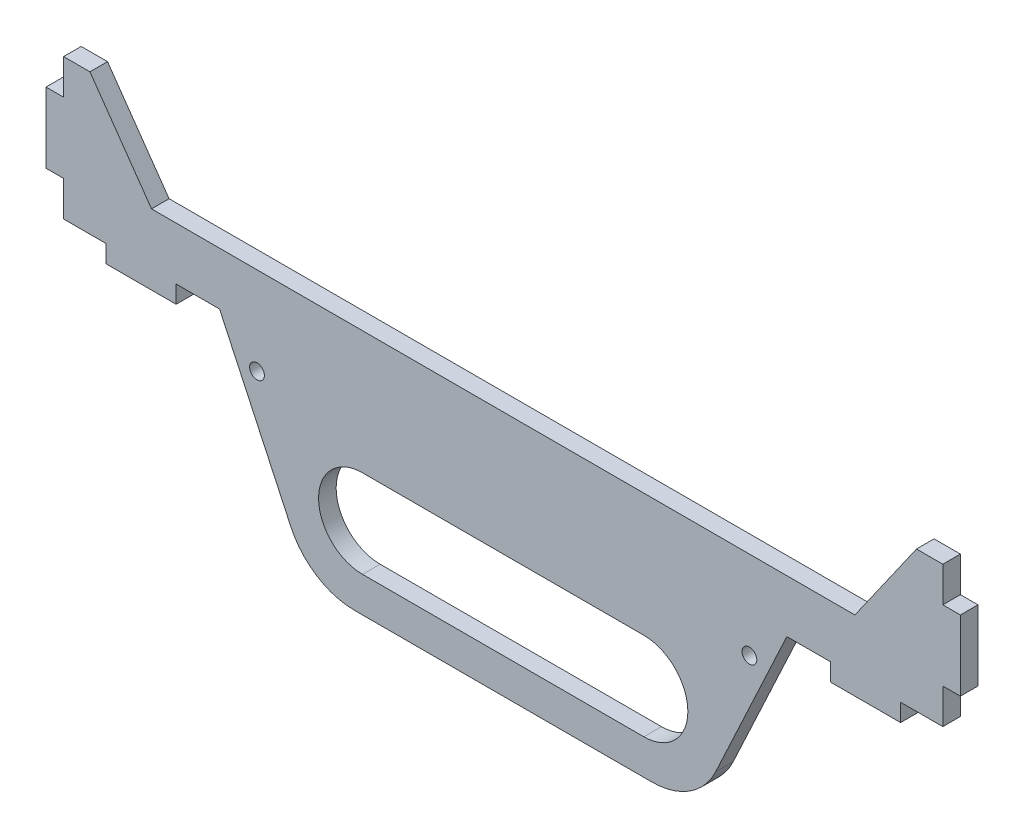
SolidWorks part; units mm, degrees
ref_plane "Front Plane" through (0, 0, 0) normal (0, 0, 1) x (1, 0, 0)
ref_plane "Top Plane" through (0, 0, 0) normal (0, 1, 0) x (1, 0, 0)
ref_plane "Right Plane" through (0, 0, 0) normal (1, 0, 0) x (0, 0, -1)
sketch "Sketch1" plane through (0, 0, 0) normal (0, 0, 1) x (1, 0, 0)
  line L0 (0, 0) -> (7.4948, 0)
  line L2 (7.4948, 0) -> (25, -25)
  line L3 (25, -25) -> (225, -25)
  line L4 (225, -25) -> (242.5052, 0)
  line L5 (242.5052, 0) -> (250, 0)
  line L7 (250, -40) -> (238, -40)
  line L9 (205.6469, -40) -> (180, -95)
  line L10 (180, -95) -> (70, -95)
  line L11 (70, -95) -> (44.3531, -40)
  line L12 (44.3531, -40) -> (32, -40)
  line L13 (0, -40) -> (0, -30)
  line L14 (0, -30) -> (-5, -30)
  line L16 (-5, -30) -> (-5, -10)
  line L17 (-5, -10) -> (0, -10)
  line L18 (0, -10) -> (0, 0)
  line L19 (250, -40) -> (250, -30)
  line L20 (250, -30) -> (255, -30)
  line L22 (255, -30) -> (255, -10)
  line L23 (255, -10) -> (250, -10)
  line L24 (250, -10) -> (250, 0)
  line L25 (85, -72.5) -> (165, -72.5) construction
  line L26 (85, -60) -> (165, -60)
  line L27 (85, -85) -> (165, -85)
  line L29 (218, -40) -> (205.6469, -40)
  line L30 (12, -40) -> (0, -40)
  line L31 (218, -40) -> (218, -45)
  line L32 (218, -45) -> (238, -45)
  line L33 (238, -40) -> (238, -45)
  line L35 (12, -40) -> (12, -45)
  line L36 (12, -45) -> (32, -45)
  line L37 (32, -40) -> (32, -45)
  arc A0 (85, -60) -> (85, -85) centre (85, -72.5) ccw
  arc A1 (165, -85) -> (165, -60) centre (165, -72.5) ccw
  point P34 (125, -72.5)
  dimension "D1" = 12.5
  dimension "D5" = 32
  dimension "D2" = 7.4948
  dimension "D3" = 12
  dimension "D4" = 25
  dimension "D6" = 44.3531
  dimension "D7" = 70
  dimension "D8" = 85
  dimension "D9" = 125
  dimension "D10" = 180
  dimension "D11" = 255
  dimension "D12" = 10
  dimension "D13" = 25
  dimension "D14" = 72.5
  dimension "D15" = 95
extrude "Boss-Extrude1" add sketch "Sketch1" along normal blind 5
fillet "Fillet1" radius 20 2 edges at (70, -95, 2.5) (180, -95, 2.5)
sketch "Sketch3" plane through (0, 0, 5) normal (0, 0, 1) x (1, 0, 0)
  line L0 (225, -25) -> (25, -25) construction
  line L1 (0, -50.4333) -> (0, -20.4333) construction
  circle A0 centre (55, -50) radius 2.1
  circle A1 centre (55, -50) radius 4 construction
  dimension "D1" = 4.2
  dimension "D2" = 8
  dimension "D3" = 25
  dimension "D4" = 55
extrude "Cut-Extrude1" cut sketch "Sketch3" against normal blind 5
ref_plane "Plane1" through (125, 0, 0) normal (-1, 0, 0) x (0, 0, 1)
mirror "Mirror1" about plane through (125, 0, 0) normal (-1, 0, 0) of "Cut-Extrude1"
